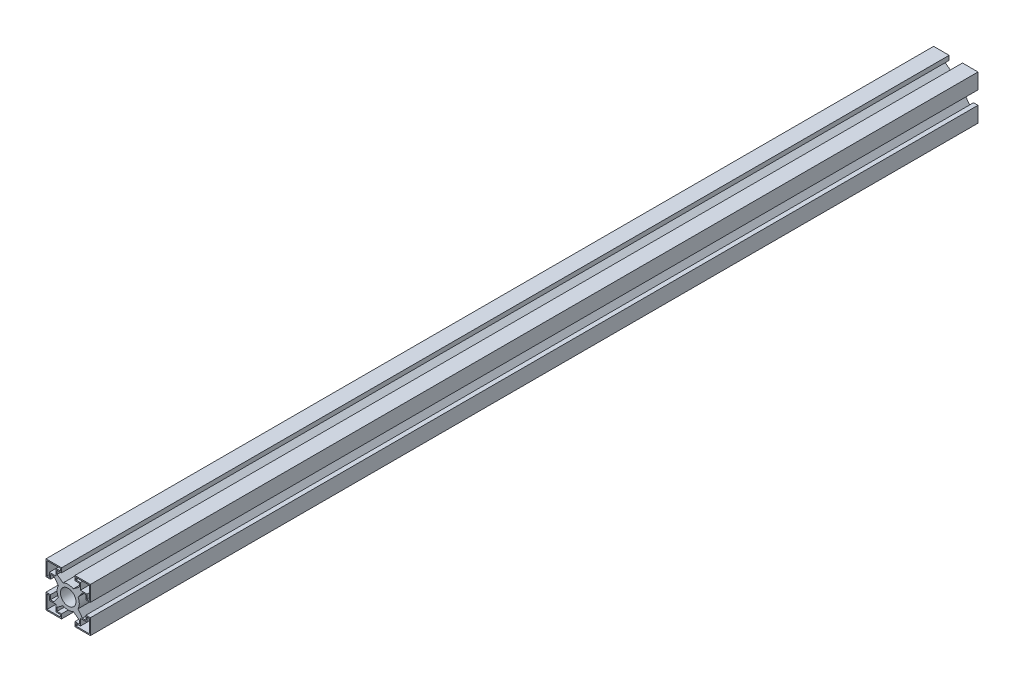
SolidWorks part; units mm, degrees
ref_plane "Plan de face" through (0, 0, 0) normal (0, 0, 1) x (1, 0, 0)
ref_plane "Plan de dessus" through (0, 0, 0) normal (0, 1, 0) x (1, 0, 0)
ref_plane "Plan de droite" through (0, 0, 0) normal (1, 0, 0) x (0, 0, -1)
sketch "Esquisse1" plane through (0, 0, 0) normal (0, 0, 1) x (1, 0, 0)
  line L5 (-5, 5) -> (-5, 1.5)
  line L22 (5, -5) -> (-5, -5) construction
  line L23 (5, -5) -> (5, 5) construction
  line L24 (5, 5) -> (-5, 5) construction
  line L25 (-5, -5) -> (-5, 5) construction
  line L26 (5, -5) -> (-5, 5) construction
  line L27 (5, 5) -> (-5, -5) construction
  line L28 (-5, 1.5) -> (-4, 1.5)
  line L29 (-4, 1.5) -> (-4, 2.5)
  line L30 (-4, 2.5) -> (-2.5, 2.5)
  line L79 (-2.5, 2.5) -> (-2.5, 4)
  line L80 (-2.5, 4) -> (-1.5, 4)
  line L82 (-1.5, 4) -> (-1.5, 5)
  line L85 (-1.5, 5) -> (-5, 5)
  line L86 (-4.75, 4.75) -> (-4.75, 1.75)
  line L87 (-4.75, 1.75) -> (-4.25, 1.75)
  line L88 (-4.25, 1.75) -> (-4.25, 2.75)
  line L89 (-4.25, 2.75) -> (-2.75, 2.75)
  line L90 (-2.75, 2.75) -> (-2.75, 4.25)
  line L92 (-2.75, 4.25) -> (-1.75, 4.25)
  line L93 (-1.75, 4.25) -> (-1.75, 4.75)
  line L94 (-1.75, 4.75) -> (-4.75, 4.75)
  line L95 (5, 5) -> (1.5, 5)
  line L96 (1.5, 5) -> (1.5, 4)
  line L97 (1.5, 4) -> (2.5, 4)
  line L98 (2.5, 4) -> (2.5, 2.5)
  line L99 (2.5, 2.5) -> (4, 2.5)
  line L100 (4, 2.5) -> (4, 1.5)
  line L101 (4, 1.5) -> (5, 1.5)
  line L102 (5, 1.5) -> (5, 5)
  line L103 (4.75, 4.75) -> (1.75, 4.75)
  line L104 (1.75, 4.75) -> (1.75, 4.25)
  line L105 (1.75, 4.25) -> (2.75, 4.25)
  line L106 (2.75, 4.25) -> (2.75, 2.75)
  line L107 (2.75, 2.75) -> (4.25, 2.75)
  line L108 (4.25, 2.75) -> (4.25, 1.75)
  line L109 (4.25, 1.75) -> (4.75, 1.75)
  line L110 (4.75, 1.75) -> (4.75, 4.75)
  line L111 (5, -5) -> (5, -1.5)
  line L112 (5, -1.5) -> (4, -1.5)
  line L113 (4, -1.5) -> (4, -2.5)
  line L114 (4, -2.5) -> (2.5, -2.5)
  line L115 (2.5, -2.5) -> (2.5, -4)
  line L116 (2.5, -4) -> (1.5, -4)
  line L117 (1.5, -4) -> (1.5, -5)
  line L118 (1.5, -5) -> (5, -5)
  line L119 (4.75, -4.75) -> (4.75, -1.75)
  line L120 (4.75, -1.75) -> (4.25, -1.75)
  line L121 (4.25, -1.75) -> (4.25, -2.75)
  line L122 (4.25, -2.75) -> (2.75, -2.75)
  line L123 (2.75, -2.75) -> (2.75, -4.25)
  line L124 (2.75, -4.25) -> (1.75, -4.25)
  line L125 (1.75, -4.25) -> (1.75, -4.75)
  line L126 (1.75, -4.75) -> (4.75, -4.75)
  line L127 (-5, -5) -> (-1.5, -5)
  line L128 (-1.5, -5) -> (-1.5, -4)
  line L129 (-1.5, -4) -> (-2.5, -4)
  line L130 (-2.5, -4) -> (-2.5, -2.5)
  line L131 (-2.5, -2.5) -> (-4, -2.5)
  line L132 (-4, -2.5) -> (-4, -1.5)
  line L133 (-4, -1.5) -> (-5, -1.5)
  line L134 (-5, -1.5) -> (-5, -5)
  line L135 (-4.75, -4.75) -> (-1.75, -4.75)
  line L136 (-1.75, -4.75) -> (-1.75, -4.25)
  line L137 (-1.75, -4.25) -> (-2.75, -4.25)
  line L138 (-2.75, -4.25) -> (-2.75, -2.75)
  line L139 (-2.75, -2.75) -> (-4.25, -2.75)
  line L140 (-4.25, -2.75) -> (-4.25, -1.75)
  line L141 (-4.25, -1.75) -> (-4.75, -1.75)
  line L142 (-4.75, -1.75) -> (-4.75, -4.75)
  line L143 (-3.2071, 2.5) -> (-2.2167, 1.156)
  line L144 (-2.5, 3.2071) -> (-1.156, 2.2167)
  line L145 (-2.2167, 1.156) -> (-1.156, 2.2167) construction
  line L146 (-2.5, 3.2071) -> (-3.2071, 2.5) construction
  line L147 (3.2071, 2.5) -> (2.2167, 1.156)
  line L148 (2.5, 3.2071) -> (1.156, 2.2167)
  line L149 (2.5, -3.2071) -> (1.156, -2.2167)
  line L150 (3.2071, -2.5) -> (2.2167, -1.156)
  line L151 (-3.2071, -2.5) -> (-2.2167, -1.156)
  line L152 (-2.5, -3.2071) -> (-1.156, -2.2167)
  circle A2 centre (0, 0) radius 1.75
  circle A3 centre (0, 0) radius 2.5
  point P73 (0, 0)
  point P78 (-2.8536, 2.8536)
  point P79 (-1.6863, 1.6863)
  point P91 (0, 0)
  dimension "D2" = 3.5
  dimension "D3" = 10
  dimension "D1" = 5
  dimension "D4" = 3.5
  dimension "D5" = 1
  dimension "D6" = 1.5
  dimension "D7" = 0.25
  dimension "D8" = 4
  dimension "D9" = 1
  dimension "D10" = 1.5
extrude "Boss.-Extru.1" add sketch "Esquisse1" along normal blind 200
